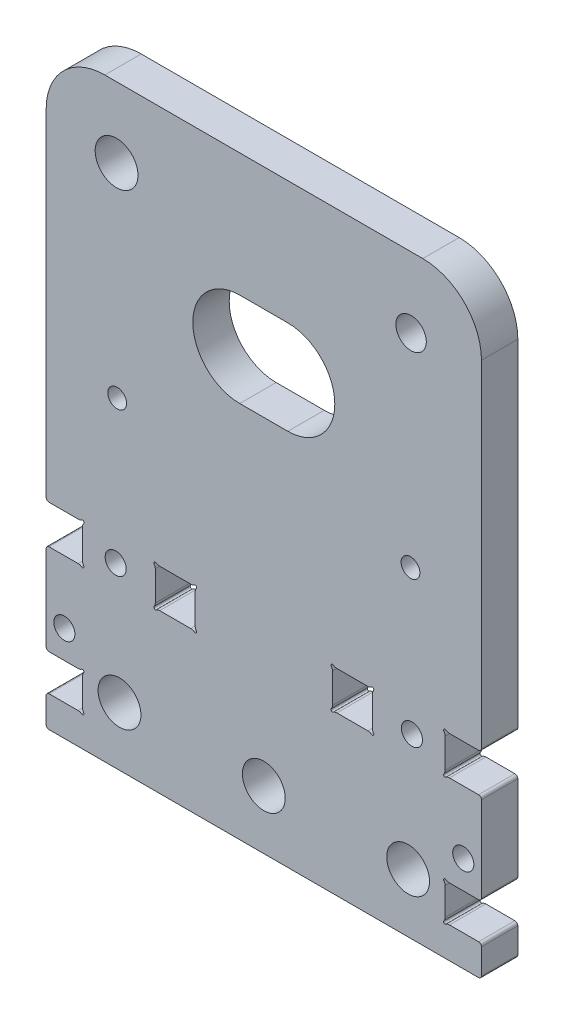
SolidWorks part; units mm, degrees
ref_plane "Front Plane" through (0, 0, 0) normal (0, 0, 1) x (1, 0, 0)
ref_plane "Top Plane" through (0, 0, 0) normal (0, 1, 0) x (1, 0, 0)
ref_plane "Right Plane" through (0, 0, 0) normal (1, 0, 0) x (0, 0, -1)
sketch "Sketch1" plane through (0, 0, 0) normal (0, 0, 1) x (1, 0, 0)
  line L0 (37.1, 0) -> (37.1, 59.3195) construction
  line L1 (0, 0) -> (74.2, 0)
  line L2 (0, 0) -> (0, 91.4)
  line L3 (10, 101.4) -> (64.2, 101.4)
  line L4 (74.2, 0) -> (74.2, 91.4)
  line L5 (0, 33.56) -> (74.2, 33.56) construction
  line L6 (-39.7056, 27) -> (34.4944, 27) construction
  line L7 (-40.5255, 5.3) -> (33.6745, 5.3) construction
  line L8 (-40.5255, 11.5) -> (33.6745, 11.5) construction
  line L9 (6.2, 79.4078) -> (6.2, -49920.5922) construction
  line L10 (68, 91.5017) -> (68, -49908.4983) construction
  line L11 (25.4, 75.1031) -> (25.4, -49924.8969) construction
  line L12 (18.6, 65.674) -> (18.6, -49934.326) construction
  line L13 (55.6, 36.7715) -> (55.6, -49963.2285) construction
  line L14 (48.8, 26.3174) -> (48.8, -49973.6826) construction
  line L16 (0, 33.56) -> (6.2, 33.56)
  line L17 (0, 33.56) -> (0, 27)
  line L18 (0, 27) -> (6.2, 27)
  line L19 (6.2, 33.56) -> (6.2, 27)
  line L20 (18.6, 33.56) -> (25.4, 33.56)
  line L21 (18.6, 33.56) -> (18.6, 27)
  line L22 (18.6, 27) -> (25.4, 27)
  line L23 (25.4, 33.56) -> (25.4, 27)
  line L24 (48.8, 33.56) -> (55.6, 33.56)
  line L25 (48.8, 33.56) -> (48.8, 27)
  line L26 (48.8, 27) -> (55.6, 27)
  line L27 (55.6, 33.56) -> (55.6, 27)
  line L28 (68, 33.56) -> (74.2, 33.56)
  line L29 (68, 33.56) -> (68, 27)
  line L30 (68, 27) -> (74.2, 27)
  line L31 (74.2, 33.56) -> (74.2, 27)
  line L32 (74.2, 5.3) -> (68, 5.3)
  line L33 (74.2, 5.3) -> (74.2, 11.5)
  line L34 (74.2, 11.5) -> (68, 11.5)
  line L35 (68, 5.3) -> (68, 11.5)
  line L36 (6.2, 11.5) -> (0, 11.5)
  line L37 (6.2, 11.5) -> (6.2, 5.3)
  line L38 (6.2, 5.3) -> (0, 5.3)
  line L39 (0, 11.5) -> (0, 5.3)
  arc A0 (64.2, 101.4) -> (74.2, 91.4) centre (64.2, 91.4) cw
  arc A1 (0, 91.4) -> (10, 101.4) centre (10, 91.4) cw
  circle A2 centre (12, 89.4) radius 3.65
  circle A3 centre (62.2, 89.4) radius 2.6
  circle A4 centre (37.1, 10) radius 3.65
  circle A5 centre (12.5, 10) radius 3.65
  circle A6 centre (61.7, 10) radius 3.65
  circle A7 centre (12.1, 54.75) radius 1.6
  circle A8 centre (62.1, 54.75) radius 1.6
  circle A9 centre (11.85, 30.28) radius 1.8
  circle A10 centre (3.1, 16.28) radius 1.8
  circle A11 centre (71.1, 16.28) radius 1.8
  circle A12 centre (62.35, 30.28) radius 1.8
  point P9 (0, 101.4)
  point P16 (37.1, 0)
  point P75 (6.2, 30.28)
  point P76 (3.1, 11.5)
  dimension "D3" = 10
  dimension "D8" = 7.3
  dimension "D9" = 5.2
  dimension "D11" = 6.2
  dimension "D12" = 6.2
  dimension "D14" = 3.2
  dimension "D27" = 3.6
  dimension "D28" = 7.3
  dimension "D1" = 74.2
  dimension "D2" = 101.4
  dimension "D4" = 12
  dimension "D5" = 12
  dimension "D6" = 12
  dimension "D7" = 12
  dimension "D10" = 10
  dimension "D13" = 49.2
  dimension "D15" = 50
  dimension "D16" = 54.75
  dimension "D17" = 6.8
  dimension "D18" = 6.8
  dimension "D19" = 12.4
  dimension "D20" = 12.4
  dimension "D21" = 5.3
  dimension "D22" = 6.2
  dimension "D23" = 15.5
  dimension "D24" = 6.56
  dimension "D25" = 16.28
  dimension "D26" = 50.5
extrude "Boss-Extrude1" add sketch "Sketch1" along normal blind 6.2 contours A1 L2 L16 L19 L18 L36 L37 L38 L1 L4 L32 L35 L34 L30 L29 L28 A0 L3 A11 A10 A9 A6 A5 A4 A3 A2 L20 L23 L22 L21 L24 L27 L26 L25 A7
sketch "Sketch2" plane through (0, 0, 6.2) normal (0, 0, 1) x (1, 0, 0)
  line L0 (33, 72.4) -> (41.2, 72.4) construction
  line L1 (33, 80.4) -> (41.2, 80.4)
  line L2 (33, 64.4) -> (41.2, 64.4)
  line L3 (74.2, 33.56) -> (74.2, 91.4) construction
  line L4 (0, 33.56) -> (0, 91.4) construction
  line L5 (10, 101.4) -> (64.2, 101.4) construction
  arc A0 (33, 80.4) -> (33, 64.4) centre (33, 72.4) ccw
  arc A1 (41.2, 64.4) -> (41.2, 80.4) centre (41.2, 72.4) ccw
  point P2 (37.1, 72.4)
  dimension "D1" = 8
  dimension "D2" = 33
  dimension "D3" = 33
  dimension "D4" = 29
extrude "Cut-Extrude1" cut sketch "Sketch2" against normal through all
sketch "Sketch3" plane through (0, 0, 6.2) normal (0, 0, 1) x (1, 0, 0)
  circle A0 centre (6.2, 33.56) radius 0.25
  circle A1 centre (6.2, 27) radius 0.25
  circle A2 centre (6.2, 11.5) radius 0.25
  circle A3 centre (6.2, 5.3) radius 0.25
  circle A4 centre (25.4, 27) radius 0.25
  circle A5 centre (18.6, 27) radius 0.25
  circle A6 centre (18.6, 33.56) radius 0.25
  circle A7 centre (25.4, 33.56) radius 0.25
  circle A8 centre (48.8, 33.56) radius 0.25
  circle A9 centre (48.8, 27) radius 0.25
  circle A10 centre (55.6, 33.56) radius 0.25
  circle A11 centre (55.6, 27) radius 0.25
  circle A12 centre (68, 33.56) radius 0.25
  circle A13 centre (68, 27) radius 0.25
  circle A14 centre (68, 11.5) radius 0.25
  circle A15 centre (68, 5.3) radius 0.25
  dimension "D1" = 0.5
extrude "Cut-Extrude2" cut sketch "Sketch3" against normal through all
fillet "Fillet1" radius 1 32 edges at (5.95, 11.5, 3.1) (6.2, 11.25, 3.1) (6.2, 5.55, 3.1) (5.95, 5.3, 3.1) (68, 5.55, 3.1) (68.25, 5.3, 3.1) (68, 11.25, 3.1) (68.25, 11.5, 3.1) (68.25, 33.56, 3.1) (68, 33.31, 3.1) (68, 27.25, 3.1) (68.25, 27, 3.1) (48.8, 27.25, 3.1) (48.8, 33.31, 3.1) (49.05, 33.56, 3.1) (55.35, 33.56, 3.1) (55.6, 33.31, 3.1) (55.6, 27.25, 3.1) (55.35, 27, 3.1) (49.05, 27, 3.1) (18.6, 27.25, 3.1) (18.85, 27, 3.1) (25.15, 27, 3.1) (25.4, 27.25, 3.1) (25.4, 33.31, 3.1) (25.15, 33.56, 3.1) (18.85, 33.56, 3.1) (18.6, 33.31, 3.1) (5.95, 33.56, 3.1) (6.2, 33.31, 3.1) (6.2, 27.25, 3.1) (5.95, 27, 3.1)
fillet "Fillet2" radius 0.5 10 edges at (0, 0, 3.1) (74.2, 0, 3.1) (74.2, 33.56, 3.1) (74.2, 27, 3.1) (74.2, 5.3, 3.1) (74.2, 11.5, 3.1) (0, 5.3, 3.1) (0, 11.5, 3.1) (0, 33.56, 3.1) (0, 27, 3.1)
